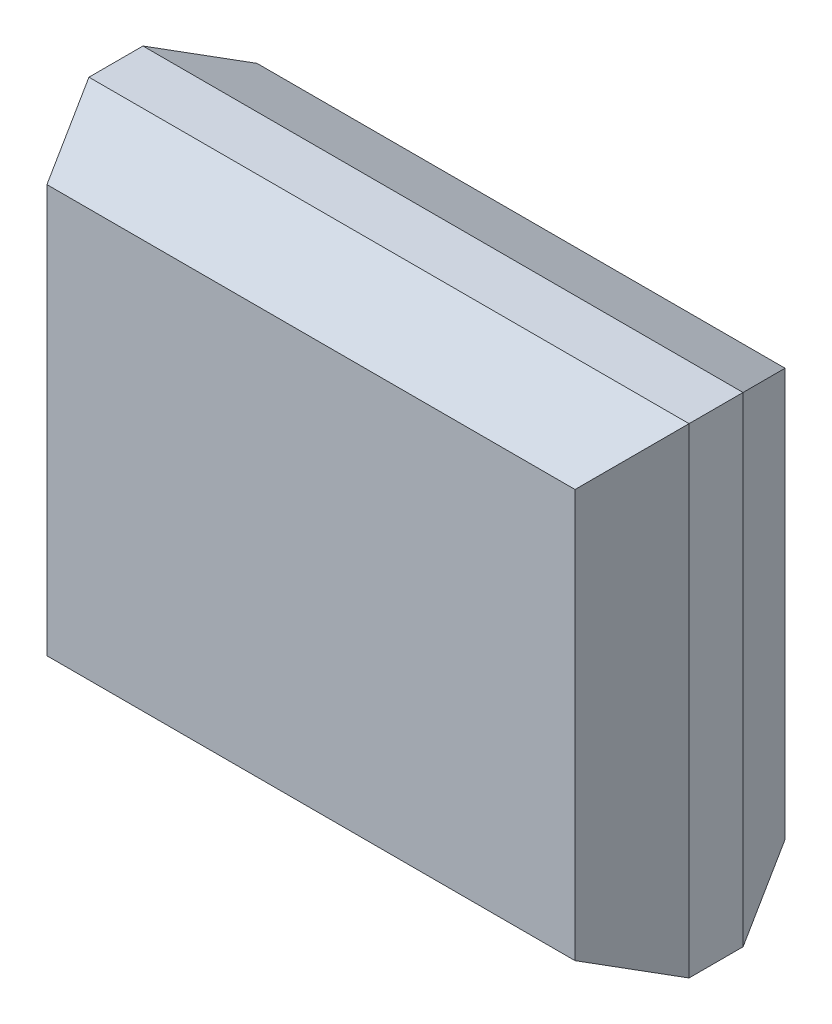
SolidWorks part; units mm, degrees
ref_plane "Plan de face" through (0, 0, 0) normal (0, 0, 1) x (1, 0, 0)
ref_plane "Plan de dessus" through (0, 0, 0) normal (0, 1, 0) x (1, 0, 0)
ref_plane "Plan de droite" through (0, 0, 0) normal (1, 0, 0) x (0, 0, -1)
sketch "Esquisse1" plane through (0, 0, 0) normal (0, 0, 1) x (1, 0, 0)
  line L1 (0, 0) -> (5, 0)
  line L2 (0, 0) -> (0, 4)
  line L3 (0, 4) -> (5, 4)
  line L4 (5, 0) -> (5, 4)
extrude "Boss.-Extru.1" add sketch "Esquisse1" along normal blind 1.75
chamfer "Chanfrein1" distance 0.65 distance2 0.3 1 edges at (2.5, 0, 1.75)
chamfer "Chanfrein2" distance 0.3 distance2 0.65 1 edges at (2.5, 0, 0)
chamfer "Chanfrein3" distance 0.65 distance2 0.3 1 edges at (2.5, 4, 1.75)
chamfer "Chanfrein4" distance 0.3 distance2 0.65 1 edges at (2.5, 4, 0)
chamfer "Chanfrein5" distance 0.65 distance2 0.3 1 edges at (0, 2, 1.75)
chamfer "Chanfrein6" distance 0.3 distance2 0.65 1 edges at (0, 2, 0)
chamfer "Chanfrein7" distance 0.65 distance2 0.3 1 edges at (5, 2, 1.75)
chamfer "Chanfrein8" distance 0.3 distance2 0.65 1 edges at (5, 2, 0)
